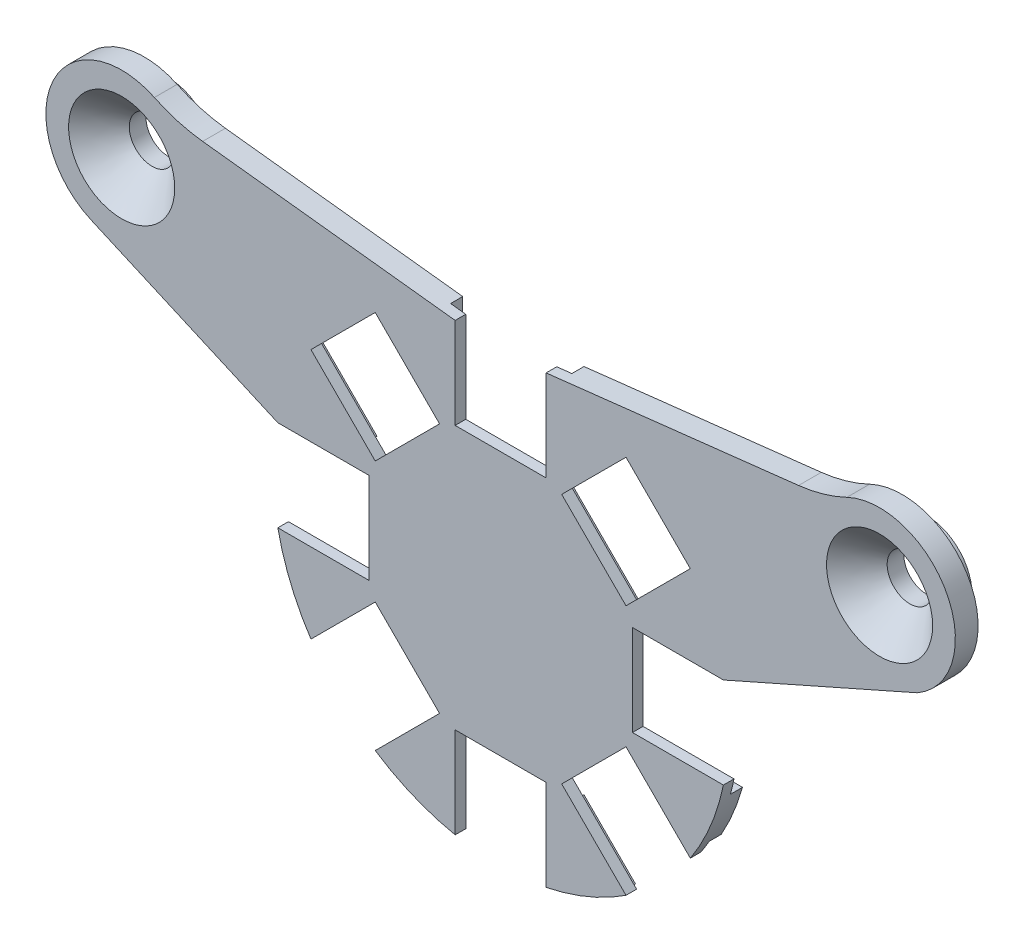
SolidWorks part; units mm, degrees
ref_plane "Спереди" through (0, 0, 0) normal (0, 0, 1) x (1, 0, 0)
ref_plane "Сверху" through (0, 0, 0) normal (0, 1, 0) x (1, 0, 0)
ref_plane "Справа" through (0, 0, 0) normal (1, 0, 0) x (0, 0, -1)
other "Configuration Table"
sketch "Эскиз1" plane through (0, 0, 0) normal (0, 0, 1) x (1, 0, 0)
  line L0 (4.0283, 8.271) -> (8.271, 4.0283)
  line L3 (0, 0) -> (0, 14.6969) construction
  line L5 (-3, 14.6969) -> (-3, 8.6969)
  line L6 (-3, 8.6969) -> (3, 8.6969)
  line L7 (3, 14.6969) -> (3, 8.6969)
  line L8 (-3, 14.6969) -> (3, 8.6969) construction
  line L9 (-3, 8.6969) -> (3, 14.6969) construction
  line L10 (8.271, 12.5136) -> (4.0283, 8.271)
  line L12 (12.5136, 8.271) -> (8.271, 4.0283)
  line L13 (8.6969, 3) -> (8.6969, -3)
  line L14 (14.6969, 3) -> (8.6969, 3)
  line L16 (14.6969, -3) -> (8.6969, -3)
  line L17 (8.271, -4.0283) -> (4.0283, -8.271)
  line L18 (12.5136, -8.271) -> (8.271, -4.0283)
  line L20 (8.271, -12.5136) -> (4.0283, -8.271)
  line L21 (3, -8.6969) -> (-3, -8.6969)
  line L22 (3, -14.6969) -> (3, -8.6969)
  line L24 (-3, -14.6969) -> (-3, -8.6969)
  line L25 (-4.0283, -8.271) -> (-8.271, -4.0283)
  line L26 (-8.271, -12.5136) -> (-4.0283, -8.271)
  line L28 (-12.5136, -8.271) -> (-8.271, -4.0283)
  line L29 (-8.6969, -3) -> (-8.6969, 3)
  line L30 (-14.6969, -3) -> (-8.6969, -3)
  line L32 (-14.6969, 3) -> (-8.6969, 3)
  line L33 (-8.271, 4.0283) -> (-4.0283, 8.271)
  line L34 (-12.5136, 8.271) -> (-8.271, 4.0283)
  line L36 (-8.271, 12.5136) -> (-4.0283, 8.271)
  line L37 (-19.6571, 16.5948) -> (-3, 14.6969)
  line L38 (3, 14.6969) -> (19.6571, 16.5948)
  line L39 (-14.6969, 3) -> (-27.015, 8.424)
  line L40 (14.6969, 3) -> (27.4936, 8.6662)
  line L41 (-12.5136, 8.271) -> (-8.271, 12.5136)
  line L42 (8.271, 12.5136) -> (12.5136, 8.271)
  line L43 (-3, 14.6969) -> (3, 14.6969)
  arc A0 (-12.5136, 8.271) -> (-14.6969, 3) centre (0, 0) ccw
  circle A3 centre (-25, 13) radius 1.5
  circle A4 centre (25, 13) radius 1.5
  arc A5 (-3, 14.6969) -> (-8.271, 12.5136) centre (0, 0) ccw
  arc A6 (8.271, 12.5136) -> (3, 14.6969) centre (0, 0) ccw
  arc A7 (14.6969, 3) -> (12.5136, 8.271) centre (0, 0) ccw
  arc A8 (12.5136, -8.271) -> (14.6969, -3) centre (0, 0) ccw
  arc A9 (3, -14.6969) -> (8.271, -12.5136) centre (0, 0) ccw
  arc A10 (-8.271, -12.5136) -> (-3, -14.6969) centre (0, 0) ccw
  arc A11 (-14.6969, -3) -> (-12.5136, -8.271) centre (0, 0) ccw
  arc A12 (-22.8417, 17.5102) -> (-27.015, 8.424) centre (-25, 13) ccw
  arc A13 (27.4936, 8.6662) -> (22.8417, 17.5102) centre (25, 13) ccw
  arc A14 (22.8417, 17.5102) -> (19.6571, 16.5948) centre (18.525, 26.5305) cw
  arc A15 (-22.8417, 17.5102) -> (-19.6571, 16.5948) centre (-18.525, 26.5305) ccw
  point P3 (0, 11.6969)
  point P44 (0, 0)
  dimension "D1" = 30
  dimension "D4" = 3
  dimension "D6" = 10
  dimension "D7" = 10
  dimension "D9" = 10
  dimension "D2" = 8
  dimension "D3" = 6
  dimension "D5" = 50
  dimension "D8" = 13
  dimension "D10" = 3
extrude "Бобышка-Вытянуть1" add sketch "Эскиз1" along normal blind 1.5
sketch "Эскиз3" plane through (0, 0, 0) normal (0, 0, -1) x (-1, 0, 0)
  line L0 (-3, 14.6969) -> (-3, 8.6969) construction
  line L1 (-4, 15.1373) -> (4, 15.1373)
  line L2 (-4, 15.1373) -> (-4, 7.6969)
  line L3 (-4, 7.6969) -> (4, 7.6969)
  line L4 (4, 15.1373) -> (4, 7.6969)
  line L5 (-4, 15.1373) -> (4, 7.6969) construction
  line L6 (-4, 7.6969) -> (4, 15.1373) construction
  line L7 (3, 14.6969) -> (3, 8.6969) construction
  line L8 (3, 8.6969) -> (-3, 8.6969) construction
  line L9 (7.8753, 13.5321) -> (13.5321, 7.8753)
  line L10 (7.8753, 13.5321) -> (2.6141, 8.271)
  line L11 (2.6141, 8.271) -> (8.271, 2.6141)
  line L12 (13.5321, 7.8753) -> (8.271, 2.6141)
  line L13 (7.8753, 13.5321) -> (8.271, 2.6141) construction
  line L14 (2.6141, 8.271) -> (13.5321, 7.8753) construction
  line L15 (15.1373, 4) -> (15.1373, -4)
  line L16 (15.1373, 4) -> (7.6969, 4)
  line L17 (7.6969, 4) -> (7.6969, -4)
  line L18 (15.1373, -4) -> (7.6969, -4)
  line L19 (15.1373, 4) -> (7.6969, -4) construction
  line L20 (7.6969, 4) -> (15.1373, -4) construction
  line L21 (13.5321, -7.8753) -> (7.8753, -13.5321)
  line L22 (13.5321, -7.8753) -> (8.271, -2.6141)
  line L23 (8.271, -2.6141) -> (2.6141, -8.271)
  line L24 (7.8753, -13.5321) -> (2.6141, -8.271)
  line L25 (13.5321, -7.8753) -> (2.6141, -8.271) construction
  line L26 (8.271, -2.6141) -> (7.8753, -13.5321) construction
  line L27 (4, -15.1373) -> (-4, -15.1373)
  line L28 (4, -15.1373) -> (4, -7.6969)
  line L29 (4, -7.6969) -> (-4, -7.6969)
  line L30 (-4, -15.1373) -> (-4, -7.6969)
  line L31 (4, -15.1373) -> (-4, -7.6969) construction
  line L32 (4, -7.6969) -> (-4, -15.1373) construction
  line L33 (-7.8753, -13.5321) -> (-13.5321, -7.8753)
  line L34 (-7.8753, -13.5321) -> (-2.6141, -8.271)
  line L35 (-2.6141, -8.271) -> (-8.271, -2.6141)
  line L36 (-13.5321, -7.8753) -> (-8.271, -2.6141)
  line L37 (-7.8753, -13.5321) -> (-8.271, -2.6141) construction
  line L38 (-2.6141, -8.271) -> (-13.5321, -7.8753) construction
  line L39 (-15.1373, -4) -> (-15.1373, 4)
  line L40 (-15.1373, -4) -> (-7.6969, -4)
  line L41 (-7.6969, -4) -> (-7.6969, 4)
  line L42 (-15.1373, 4) -> (-7.6969, 4)
  line L43 (-15.1373, -4) -> (-7.6969, 4) construction
  line L44 (-7.6969, -4) -> (-15.1373, 4) construction
  line L45 (-13.5321, 7.8753) -> (-7.8753, 13.5321)
  line L46 (-13.5321, 7.8753) -> (-8.271, 2.6141)
  line L47 (-8.271, 2.6141) -> (-2.6141, 8.271)
  line L48 (-7.8753, 13.5321) -> (-2.6141, 8.271)
  line L49 (-13.5321, 7.8753) -> (-2.6141, 8.271) construction
  line L50 (-8.271, 2.6141) -> (-7.8753, 13.5321) construction
  point P0 (0, 11.4171)
  point P13 (8.0731, 8.0731)
  point P18 (11.4171, 0)
  point P23 (8.0731, -8.0731)
  point P28 (0, -11.4171)
  point P33 (-8.0731, -8.0731)
  point P38 (-11.4171, 0)
  point P43 (-8.0731, 8.0731)
  point P48 (0, 0)
  dimension "D1" = 1
  dimension "D2" = 1
  dimension "D3" = 1
  dimension "D4" = 8
extrude "Вырез-Вытянуть2" cut sketch "Эскиз3" against normal blind 0.8
sketch "Эскиз4" plane through (0, 0, 0) normal (0, 0, -1) x (-1, 0, 0)
  line L0 (0, 0) -> (0, 21.2157) construction
  circle A0 centre (25, 13) radius 3
  circle A1 centre (25, 13) radius 1.5
  circle A2 centre (-25, 13) radius 1.5
  circle A3 centre (-25, 13) radius 3
  dimension "D1" = 6
extrude "Бобышка-Вытянуть2" add sketch "Эскиз4" along normal blind 1.6
fillet "Скругление1" radius 1 2 edges at (-22, 13, 0) (28, 13, 0)
chamfer "Фаска1" distance 2 angle 45 2 edges at (-23.5, 13, 1.5) (26.5, 13, 1.5)
